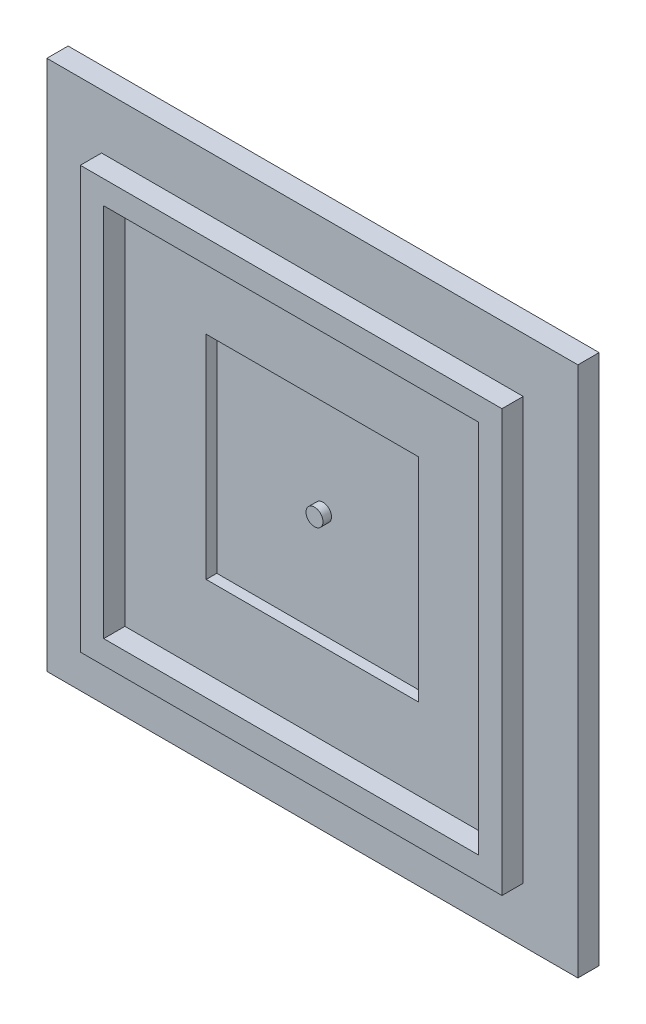
SolidWorks part; units mm, degrees
ref_plane "Front Plane" through (0, 0, 0) normal (0, 0, 1) x (1, 0, 0)
ref_plane "Top Plane" through (0, 0, 0) normal (0, 1, 0) x (1, 0, 0)
ref_plane "Right Plane" through (0, 0, 0) normal (1, 0, 0) x (0, 0, -1)
sketch "Sketch1" plane through (0, 0, 0) normal (0, 0, 1) x (1, 0, 0)
  line L1 (63.5, 63.5) -> (-63.5, 63.5)
  line L2 (63.5, 63.5) -> (63.5, -63.5)
  line L3 (63.5, -63.5) -> (-63.5, -63.5)
  line L4 (-63.5, 63.5) -> (-63.5, -63.5)
  line L5 (63.5, 63.5) -> (-63.5, -63.5) construction
  line L6 (63.5, -63.5) -> (-63.5, 63.5) construction
  point P0 (0, 0)
  dimension "D1" = 127
  dimension "D2" = 127
extrude "Boss-Extrude1" add sketch "Sketch1" against normal blind 5.08
sketch "Sketch2" plane through (0, 0, 0) normal (0, 0, 1) x (1, 0, 0)
  line L1 (-50.419, 50.419) -> (50.419, 50.419)
  line L2 (-50.419, 50.419) -> (-50.419, -50.419)
  line L3 (-50.419, -50.419) -> (50.419, -50.419)
  line L4 (50.419, 50.419) -> (50.419, -50.419)
  line L5 (-50.419, 50.419) -> (50.419, -50.419) construction
  line L6 (-50.419, -50.419) -> (50.419, 50.419) construction
  point P0 (0, 0)
  dimension "D1" = 100.838
  dimension "D2" = 100.838
extrude "Boss-Extrude2" add sketch "Sketch2" along normal blind 5.08 contours L2 L1 L4 L3
sketch "Sketch3" plane through (0, 0, 5.08) normal (0, 0, 1) x (1, 0, 0)
  line L1 (-44.831, 44.831) -> (44.831, 44.831)
  line L2 (-44.831, 44.831) -> (-44.831, -44.831)
  line L3 (-44.831, -44.831) -> (44.831, -44.831)
  line L4 (44.831, 44.831) -> (44.831, -44.831)
  line L5 (-44.831, 44.831) -> (44.831, -44.831) construction
  line L6 (-44.831, -44.831) -> (44.831, 44.831) construction
  point P0 (0, 0)
  dimension "D1" = 89.662
  dimension "D2" = 89.662
extrude "Cut-Extrude1" cut sketch "Sketch3" against normal blind 5.08
sketch "Sketch8" plane through (0, 0, 0) normal (0, 0, 1) x (1, 0, 0)
  line L1 (25.4, 25.4) -> (-25.4, 25.4)
  line L2 (25.4, 25.4) -> (25.4, -25.4)
  line L3 (25.4, -25.4) -> (-25.4, -25.4)
  line L4 (-25.4, 25.4) -> (-25.4, -25.4)
  line L5 (25.4, 25.4) -> (-25.4, -25.4) construction
  line L6 (25.4, -25.4) -> (-25.4, 25.4) construction
  point P0 (0, 0)
  dimension "D1" = 50.8
  dimension "D2" = 50.8
extrude "Cut-Extrude2" cut sketch "Sketch8" against normal blind 2.54
sketch "Sketch9" plane through (0, 0, -2.54) normal (0, 0, 1) x (1, 0, 0)
  circle A0 centre (0, 0) radius 2.032
  dimension "D1" = 4.064
extrude "Boss-Extrude10" add sketch "Sketch9" along normal blind 2.032
